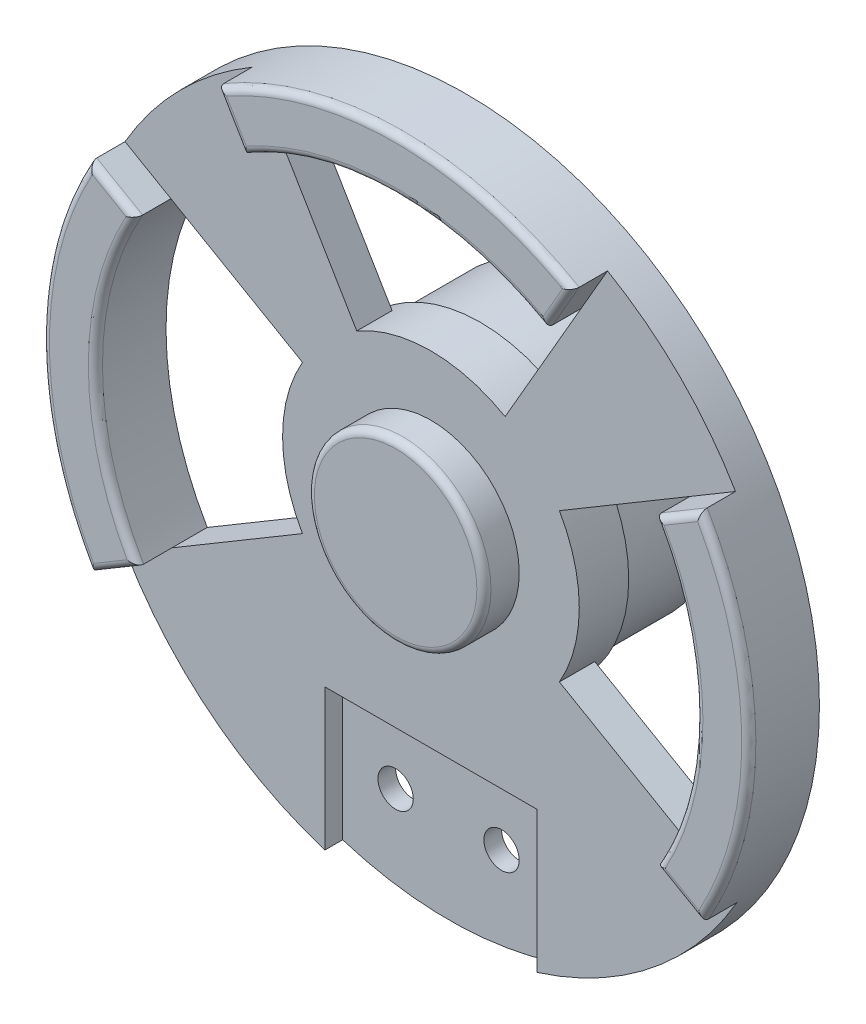
SolidWorks part; units mm, degrees
ref_plane "Front Plane" through (0, 0, 0) normal (0, 0, 1) x (1, 0, 0)
ref_plane "Top Plane" through (0, 0, 0) normal (0, 1, 0) x (1, 0, 0)
ref_plane "Right Plane" through (0, 0, 0) normal (1, 0, 0) x (0, 0, -1)
sketch "Sketch1" plane through (0, 0, 0) normal (0, 0, 1) x (1, 0, 0)
  circle A0 centre (0, 0) radius 19.875
  dimension "D1" = 39.75
extrude "Boss-Extrude1" add sketch "Sketch1" along normal blind 15
sketch "Sketch2" plane through (0, 0, 15) normal (0, 0, 1) x (1, 0, 0)
  circle A0 centre (0, 0) radius 21
  dimension "D1" = 42
extrude "Boss-Extrude2" add sketch "Sketch2" along normal blind 2
sketch "Sketch3" plane through (0, 0, 17) normal (0, 0, 1) x (1, 0, 0)
  circle A0 centre (0, 0) radius 50
  dimension "D1" = 100
extrude "Boss-Extrude3" add sketch "Sketch3" along normal blind 5
sketch "Sketch4" plane through (0, 0, 17) normal (0, 0, -1) x (-1, 0, 0)
  line L0 (0, 50) -> (0, 21) construction
  line L1 (-21, 0) -> (-50, 0) construction
  line L2 (0, 0) -> (-10.5, 18.1865) construction
  line L3 (0, 0) -> (10.5, 18.1865) construction
  line L4 (-10.5, 18.1865) -> (-21.25, 36.8061)
  line L5 (10.5, 18.1865) -> (21.4846, 36.6696)
  line L6 (18.1865, -10.5) -> (36.6696, -21.4846)
  line L7 (18.1865, 10.5) -> (36.8061, 21.25)
  line L10 (-18.1865, 10.5) -> (-36.6696, 21.4846)
  line L11 (-18.1865, -10.5) -> (-36.8061, -21.25)
  line L12 (10.5, -18.1865) -> (21.25, -36.8061) [skipped]
  line L13 (-10.5, -18.1865) -> (-21.4846, -36.6696) [skipped]
  arc A0 (-21.25, 36.8061) -> (21.4846, 36.6696) centre (0, 0) cw
  arc A1 (-10.5, 18.1865) -> (10.5, 18.1865) centre (0, 0) cw
  arc A2 (36.8061, 21.25) -> (36.6696, -21.4846) centre (0, 0) cw
  circle A3 centre (0, 0) radius 50 construction
  circle A4 centre (0, 0) radius 21 construction
  arc A5 (18.1865, 10.5) -> (18.1865, -10.5) centre (0, 0) cw
  circle A6 centre (0, 0) radius 21 construction
  arc A9 (-36.8061, -21.25) -> (-36.6696, 21.4846) centre (0, 0) cw
  arc A10 (-18.1865, -10.5) -> (-18.1865, 10.5) centre (0, 0) cw
  arc A11 (21.25, -36.8061) -> (-21.4846, -36.6696) centre (0, 0) cw [skipped]
  arc A12 (10.5, -18.1865) -> (-10.5, -18.1865) centre (0, 0) cw [skipped]
  circle M8 centre (0, 0) radius 21
  dimension "D2" = 42.5
  dimension "D1" = 30
  dimension "D3" = 4
extrude "Cut-Extrude2" cut sketch "Sketch4" against normal blind 5 contours A9 L11 L10 M8 | A0 L4 L5 M8 | A2 L7 L6 M8
sketch "Sketch5" plane through (0, 0, 22) normal (0, 0, 1) x (1, 0, 0)
  line L0 (-15, -47.697) -> (-15, -27.697)
  line L1 (-15, -27.697) -> (15, -27.697)
  line L2 (15, -27.697) -> (15, -47.697)
  circle A0 centre (0, 0) radius 50 construction
  arc A1 (-15, -47.697) -> (15, -47.697) centre (0, 0) ccw
  circle M1 centre (0, 0) radius 50
  dimension "D1" = 15
  dimension "D2" = 15
  dimension "D3" = 20
extrude "Cut-Extrude3" cut sketch "Sketch5" against normal blind 2.5 contours L2 L1 L0 M1
sketch "Sketch8" plane through (0, 0, 19.5) normal (0, 0, 1) x (1, 0, 0)
  line L0 (-15, -27.697) -> (15, -27.697) construction
  line L1 (-15, -27.697) -> (15, -27.697) construction
  circle A0 centre (-7.5, -37.697) radius 2.5
  circle A1 centre (7.5, -37.697) radius 2.5
  dimension "D1" = 5
  dimension "D2" = 5
  dimension "D3" = 7.5
  dimension "D4" = 7.5
  dimension "D5" = 10
  dimension "D6" = 10
extrude "Cut-Extrude4" cut sketch "Sketch8" against normal through all
sketch "Sketch9" plane through (0, 0, 22) normal (0, 0, 1) x (1, 0, 0)
  line L0 (-36.8061, 21.25) -> (-43.3013, 25)
  line L1 (-36.6696, -21.4846) -> (-43.117, -25.3164)
  line L2 (-21.4846, 36.6696) -> (-25.3164, 43.117)
  line L3 (21.25, 36.8061) -> (25, 43.3013)
  line L4 (36.6696, 21.4846) -> (43.117, 25.3164)
  line L5 (36.8061, -21.25) -> (43.3013, -25)
  line L9 (21.4846, -36.6696) -> (25.3164, -43.117) [skipped]
  line L10 (-21.25, -36.8061) -> (-25, -43.3013) [skipped]
  arc A0 (15, -47.697) -> (-15, -47.697) centre (0, 0) ccw construction
  arc A1 (-43.117, -25.3164) -> (-43.3013, 25) centre (0, 0) cw
  arc A2 (-36.8061, 21.25) -> (-36.6696, -21.4846) centre (0, 0) ccw
  arc A3 (21.25, 36.8061) -> (-21.4846, 36.6696) centre (0, 0) ccw
  arc A4 (-25.3164, 43.117) -> (25, 43.3013) centre (0, 0) cw
  arc A5 (36.8061, -21.25) -> (36.6696, 21.4846) centre (0, 0) ccw
  arc A6 (43.117, 25.3164) -> (43.3013, -25) centre (0, 0) cw
  arc A10 (25.3164, -43.117) -> (-25, -43.3013) centre (0, 0) cw [skipped]
  arc A11 (-21.25, -36.8061) -> (21.4846, -36.6696) centre (0, 0) ccw [skipped]
  dimension "D1" = 4
extrude "Boss-Extrude4" add sketch "Sketch9" along normal blind 5
fillet "Fillet1" radius 1 12 edges at (-39.8933, -23.4005, 27) (-49.9997, -0.1831, 27) (-40.0537, 23.125, 27) (-42.4998, -0.1357, 27) (40.0537, -23.125, 27) (42.4998, 0.1357, 27) (49.9997, 0.1831, 27) (39.8933, 23.4005, 27) (23.125, 40.0537, 27) (-0.1831, 49.9997, 27) (-23.4005, 39.8933, 27) (-0.1357, 42.4998, 27)
chamfer "Chamfer1" distance 2 angle 45 1 edges at (19.875, 0, 0)
sketch "Sketch10" plane through (0, 0, 22) normal (0, 0, 1) x (1, 0, 0)
  circle A0 centre (0, 0) radius 12.5
  dimension "D1" = 25
extrude "Boss-Extrude5" add sketch "Sketch10" along normal up to surface (5 mm away) up to face at (-0.1494, 43.3584, 27)
fillet "Fillet2" radius 1 1 edges at (12.5, 0, 27)
